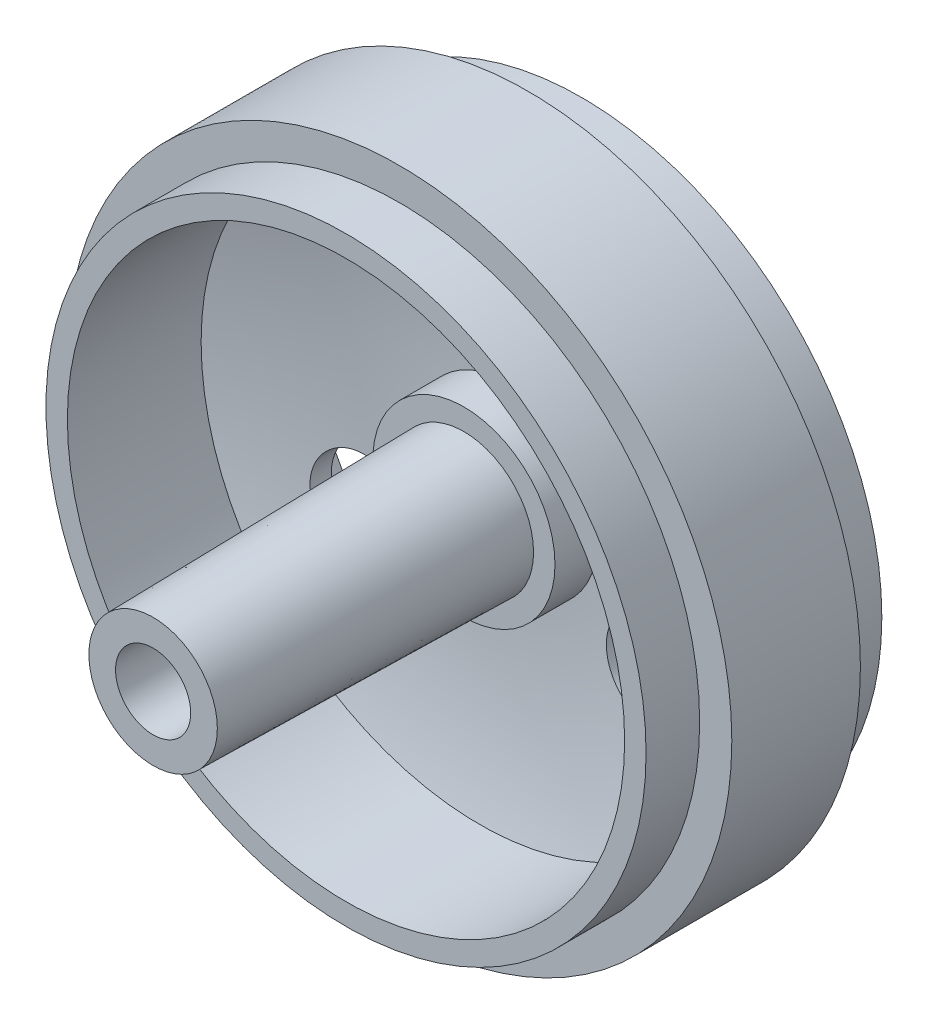
SolidWorks part; units mm, degrees
ref_plane "Front Plane" through (0, 0, 0) normal (0, 0, 1) x (1, 0, 0)
ref_plane "Top Plane" through (0, 0, 0) normal (0, 1, 0) x (1, 0, 0)
ref_plane "Right Plane" through (0, 0, 0) normal (1, 0, 0) x (0, 0, -1)
sketch "Sketch3" plane through (0, 0, 0) normal (1, 0, 0) x (0, 0, -1)
  line L0 (0, -60.6412) -> (0, 15.5) construction
  line L1 (-77.7475, 0) -> (88.9514, 0) construction
  line L2 (-5.5, 13) -> (0.74, 13)
  line L3 (5.5, 13) -> (5.5, 14)
  line L4 (5.5, 14) -> (3, 14)
  line L5 (3, 14) -> (3, 15.5)
  line L6 (3, 15.5) -> (-3, 15.5)
  line L7 (-3, 14) -> (-3, 15.5)
  line L8 (-5.5, 14) -> (-3, 14)
  line L9 (-5.5, 13) -> (-5.5, 14)
  line L10 (0, 3.25) -> (5.5, 3.25)
  line L11 (5.5, 3.25) -> (5.5, 4.25)
  line L12 (5.5, 4.25) -> (3, 4.25)
  line L14 (0, 3.25) -> (0, 4.25)
  line L16 (1.74, 13) -> (5.5, 13)
  line L17 (2, 4.25) -> (0, 4.25)
  arc A0 (1.74, 13) -> (3, 4.25) centre (-29.138, 4.0878) cw
  arc A1 (0.74, 13) -> (2, 4.25) centre (-30.138, 4.0878) cw
  point P14 (0, 13)
  point P19 (0, 4.25)
  point P20 (0, 3.25)
  point P25 (-0.9436, 13)
  dimension "D1" = 13
  dimension "D2" = 1
  dimension "D3" = 1.5
  dimension "D4" = 5.5
  dimension "D5" = 2.5
  dimension "D6" = 3.25
  dimension "D7" = 1
  dimension "D8" = 5.5
  dimension "D9" = 3.76
  dimension "D10" = 2.5
  dimension "D11" = 1
revolve "Revolve1" add sketch "Sketch3" angle 360 about L1
sketch "Sketch4" plane through (0, 0, 0) normal (0, 0, 1) x (1, 0, 0)
  circle A0 centre (0, 0) radius 3.25
  circle A1 centre (0, 0) radius 1.5
extrude "Boss-Extrude1" add sketch "Sketch4" along normal blind 14.5 draft 1 and the other way blind 1
sketch "Sketch5" plane through (0, 0, -5.5) normal (0, 0, -1) x (-1, 0, 0)
  line L0 (0, 0) -> (0, 15.5) construction
  circle A0 centre (0, 7.75) radius 2
  circle A1 centre (0, 0) radius 15.5 construction
  circle A2 centre (6.7117, -3.875) radius 2
  circle A3 centre (-6.7117, -3.875) radius 2
  point P14 (0, 0)
  dimension "D1" = 3
extrude "Cut-Extrude1" cut sketch "Sketch5" against normal blind 14.5
